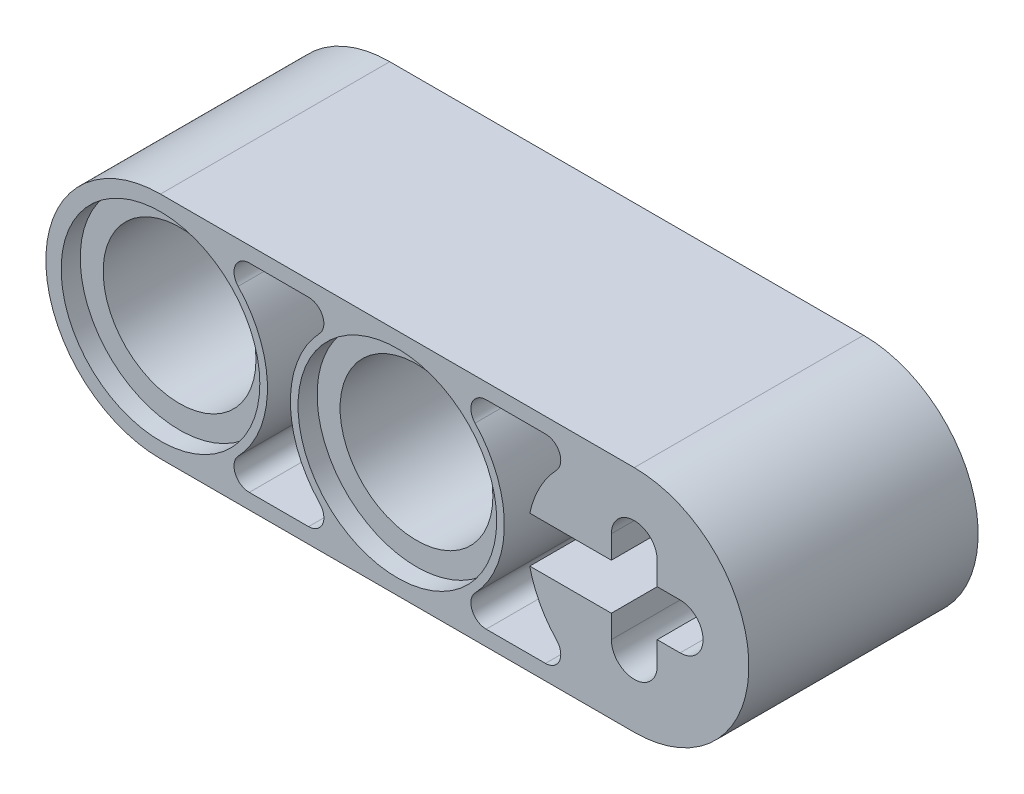
SolidWorks part; units mm, degrees
material "PVC Rigid"
ref_plane "Front Plane" through (0, 0, 0) normal (0, 0, 1) x (1, 0, 0)
ref_plane "Top Plane" through (0, 0, 0) normal (0, 1, 0) x (1, 0, 0)
ref_plane "Right Plane" through (0, 0, 0) normal (1, 0, 0) x (0, 0, -1)
sketch "Sketch1" plane through (0, 0, 0) normal (0, 0, 1) x (1, 0, 0)
  line L0 (-7.874, 0) -> (7.874, 0) construction
  line L1 (7.874, -3.81) -> (-7.874, -3.81)
  line L2 (7.874, 3.81) -> (-7.874, 3.81)
  line L8 (0, 15.1379) -> (0, -14.3507)
  line L9 (3.937, 3.302) -> (3.937, -3.302) construction
  line L10 (3.937, 3.302) -> (3.937, 3.81)
  line L11 (2.9512, -3.302) -> (4.9228, -3.302)
  line L12 (2.9512, 3.302) -> (4.9228, 3.302)
  line L13 (3.937, -3.302) -> (3.937, -3.81)
  line L14 (-3.937, 3.302) -> (-3.937, -3.302) construction
  line L15 (-3.937, -3.302) -> (-3.937, -3.81)
  line L16 (-2.9512, 3.302) -> (-4.9228, 3.302)
  line L17 (-2.9512, -3.302) -> (-4.9228, -3.302)
  line L18 (-3.937, 3.302) -> (-3.937, 3.81)
  line L19 (7.874, 1.524) -> (7.874, -1.524) construction
  line L20 (8.636, 1.524) -> (8.636, -1.524)
  line L21 (7.112, 1.524) -> (7.112, -1.524)
  line L22 (6.35, 0) -> (9.398, 0) construction
  line L23 (4.4006, 0.762) -> (9.398, 0.762)
  line L24 (4.4006, -0.762) -> (9.398, -0.762)
  arc A0 (7.874, -3.81) -> (7.874, 3.81) centre (7.874, 0) ccw
  circle A1 centre (0, 0) radius 3.302
  circle A2 centre (0, 0) radius 2.54
  circle A3 centre (7.874, 0) radius 3.302
  circle A4 centre (7.874, 0) radius 2.54
  arc A5 (-2.9512, 3.302) -> (-2.5823, 2.4447) centre (-2.9512, 2.794) cw
  arc A7 (-4.9228, 3.302) -> (-5.2917, 2.4447) centre (-4.9228, 2.794) ccw
  arc A8 (-5.2917, -2.4447) -> (-4.9228, -3.302) centre (-4.9228, -2.794) ccw
  arc A11 (2.5823, -2.4448) -> (2.5823, 2.4447) centre (0, 0) ccw
  arc A12 (5.2917, 2.4447) -> (5.2917, -2.4447) centre (7.874, 0) ccw
  arc A13 (2.5823, -2.4448) -> (2.9512, -3.302) centre (2.9512, -2.794) ccw
  arc A14 (-2.5823, -2.4448) -> (-2.9512, -3.302) centre (-2.9512, -2.794) cw
  arc A15 (-5.2917, 2.4447) -> (-5.2917, -2.4447) centre (-7.874, 0) cw
  arc A16 (5.2917, -2.4447) -> (4.9228, -3.302) centre (4.9228, -2.794) cw
  arc A17 (4.9228, 3.302) -> (5.2917, 2.4447) centre (4.9228, 2.794) cw
  arc A18 (2.9512, 3.302) -> (2.5823, 2.4447) centre (2.9512, 2.794) ccw
  arc A19 (-2.5823, -2.4448) -> (-2.5823, 2.4447) centre (0, 0) cw
  circle A20 centre (-7.874, 0) radius 2.54
  circle A21 centre (-7.874, 0) radius 3.302
  arc A22 (-7.874, -3.81) -> (-7.874, 3.81) centre (-7.874, 0) cw
  circle A23 centre (7.874, 0) radius 2.286 construction
  arc A24 (8.636, 1.524) -> (7.112, 1.524) centre (7.874, 1.524) ccw
  arc A25 (7.112, -1.524) -> (8.636, -1.524) centre (7.874, -1.524) ccw
  arc A27 (9.398, -0.762) -> (9.398, 0.762) centre (9.398, 0) ccw
  point P13 (9.525, 0)
  point P14 (0, -3.81)
  point P15 (7.62, 0)
  point P17 (0, 3.302)
  point P18 (19.05, 3.302)
  point P19 (0, -3.302)
  point P20 (19.05, -3.302)
  point P23 (13.843, 0)
  point P25 (23.368, 0)
  point P26 (3.429, 0)
  point P27 (-7.874, -3.302)
  point P28 (7.874, -3.302)
  point P29 (-7.874, 3.302)
  point P30 (7.874, 3.302)
  point P35 (11.811, 0)
  point P60 (11.5175, 1.1139)
  point P67 (0, 3.81)
  point P70 (7.874, 0)
  point P77 (7.874, 0)
  dimension "D2" = 7.62
  dimension "D3" = 0.508
  dimension "D4" = 5.08
  dimension "D6" = 11.684
  dimension "D9" = 1.524
  dimension "D1" = 0.254
  dimension "D5" = 0.508
  dimension "D7" = 4.572
  dimension "D8" = 1.524
extrude "Boss-Extrude1" add sketch "Sketch1" along normal blind 3.81
ref_plane "Plane2" through (11.684, 0, 0) normal (1, 0, 0) x (0, 0, -1)
sketch "Sketch2" plane through (0, 0, 0) normal (0, 0, 1) x (1, 0, 0)
  circle A0 centre (7.874, 0) radius 3.302 construction
  circle A2 centre (7.874, 0) radius 3.302 construction
  circle A3 centre (0, 0) radius 3.302 construction
  circle A4 centre (0, 0) radius 3.302
  circle A5 centre (-7.874, 0) radius 3.302 construction
  circle A6 centre (-7.874, 0) radius 3.302
extrude "Cut-Extrude3" cut sketch "Sketch2" along normal blind 0.635
mirror "Mirror1" about plane through (0, -22.6846, 3.81) normal (0, 0, 1) of bodies 117
ref_plane "Plane3" through (0, 0, 0) normal (0, 1, 0) x (-1, 0, 0)
